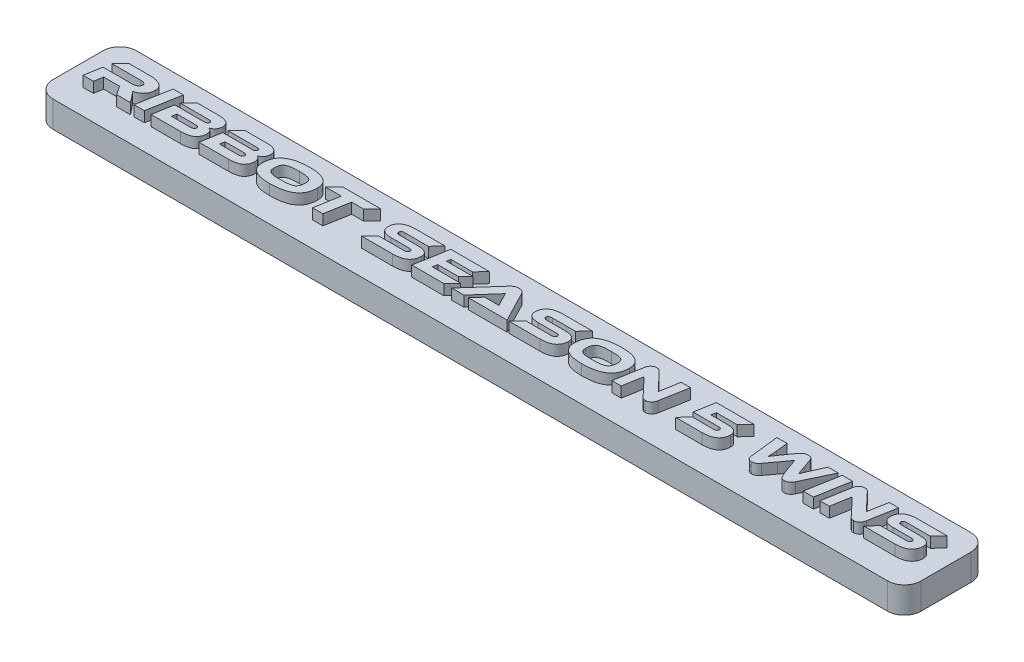
SolidWorks part; units mm, degrees
ref_plane "Front Plane" through (0, 0, 0) normal (0, 0, 1) x (1, 0, 0)
ref_plane "Top Plane" through (0, 0, 0) normal (0, 1, 0) x (1, 0, 0)
ref_plane "Right Plane" through (0, 0, 0) normal (1, 0, 0) x (0, 0, -1)
sketch "Sketch1" plane through (0, 0, 0) normal (0, 1, 0) x (1, 0, 0)
  line L0 (-82.55, -3.175) -> (82.55, -3.175) construction
  line L1 (-82.55, -7.9375) -> (82.55, -7.9375)
  line L2 (-82.55, -7.9375) -> (-82.55, 7.9375)
  line L3 (-82.55, 7.9375) -> (82.55, 7.9375)
  line L4 (82.55, -7.9375) -> (82.55, 7.9375)
  line L5 (-82.55, -7.9375) -> (82.55, 7.9375) construction
  line L6 (-82.55, 7.9375) -> (82.55, -7.9375) construction
  point P0 (0, 0)
  dimension "D1" = 165.1
  dimension "D2" = 15.875
  dimension "D3" = 4.7625
extrude "Boss-Extrude1" add sketch "Sketch1" against normal blind 5
fillet "Fillet1" radius 3.175 4 edges at (82.55, -2.5, -7.9375) (-82.55, -2.5, 7.9375) (82.55, -2.5, 7.9375) (-82.55, -2.5, -7.9375)
sketch "Sketch2" plane through (0, 0, 0) normal (0, 1, 0) x (1, 0, 0)
  line L0 (-82.55, -3.175) -> (82.55, -3.175) construction
  line L1 (82.55, -4.7625) -> (82.55, 4.7625) construction
  line L2 (-82.55, 4.7625) -> (-82.55, -4.7625) construction
  text T0 "Ribbot Season 5 Wins" font "Ethnocentric Rg" height in points 24
  dimension "D1" = 3.175
extrude "Boss-Extrude2" add sketch "Sketch2" along normal blind 2
sketch "Sketch3" plane through (0, -5, 0) normal (0, -1, 0) x (1, 0, 0)
  line L0 (-77.7875, 0) -> (0, 0) construction
  line L1 (0, 0) -> (77.7875, 0) construction
  line L2 (-82.55, -4.7625) -> (-82.55, 4.7625) construction
  circle A0 centre (-77.7875, 0) radius 0.9
  circle A1 centre (0, 0) radius 0.9
  circle A2 centre (77.7875, 0) radius 0.9
  dimension "D2" = 1.8
  dimension "D1" = 4.7625
extrude "Cut-Extrude1" cut sketch "Sketch3" against normal blind 4
